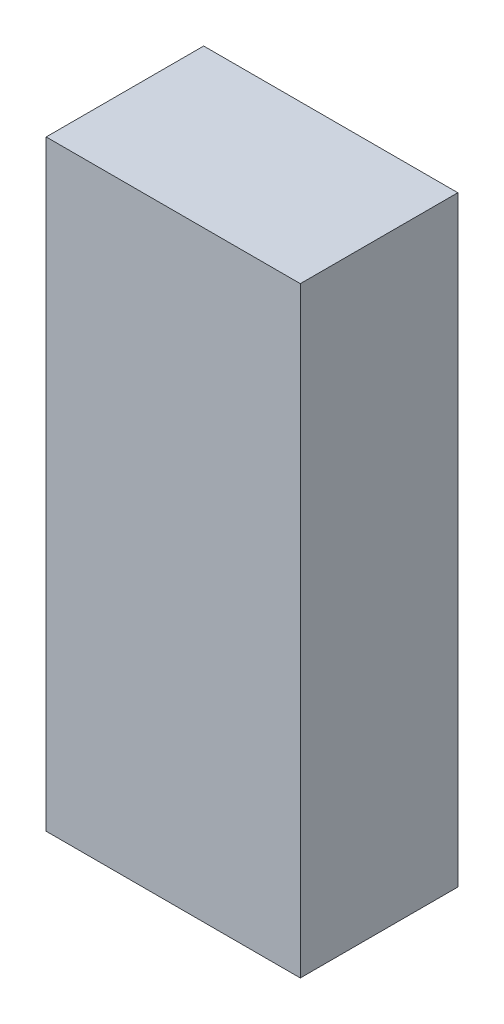
SolidWorks part; units mm, degrees
ref_plane "Front Plane" through (0, 0, 0) normal (0, 0, 1) x (1, 0, 0)
ref_plane "Top Plane" through (0, 0, 0) normal (0, 1, 0) x (1, 0, 0)
ref_plane "Right Plane" through (0, 0, 0) normal (1, 0, 0) x (0, 0, -1)
sketch "Sketch1" plane through (0, 0, 0) normal (0, 1, 0) x (1, 0, 0)
  line L1 (-450.85, -279.4) -> (450.85, -279.4)
  line L2 (-450.85, -279.4) -> (-450.85, 279.4)
  line L3 (-450.85, 279.4) -> (450.85, 279.4)
  line L4 (450.85, -279.4) -> (450.85, 279.4)
  line L5 (-450.85, -279.4) -> (450.85, 279.4) construction
  line L6 (-450.85, 279.4) -> (450.85, -279.4) construction
  point P0 (0, 0)
  dimension "D1" = 558.8
  dimension "D2" = 901.7
extrude "Boss-Extrude1" add sketch "Sketch1" along normal blind 2133.6
shell "Shell1" thickness 3.175
